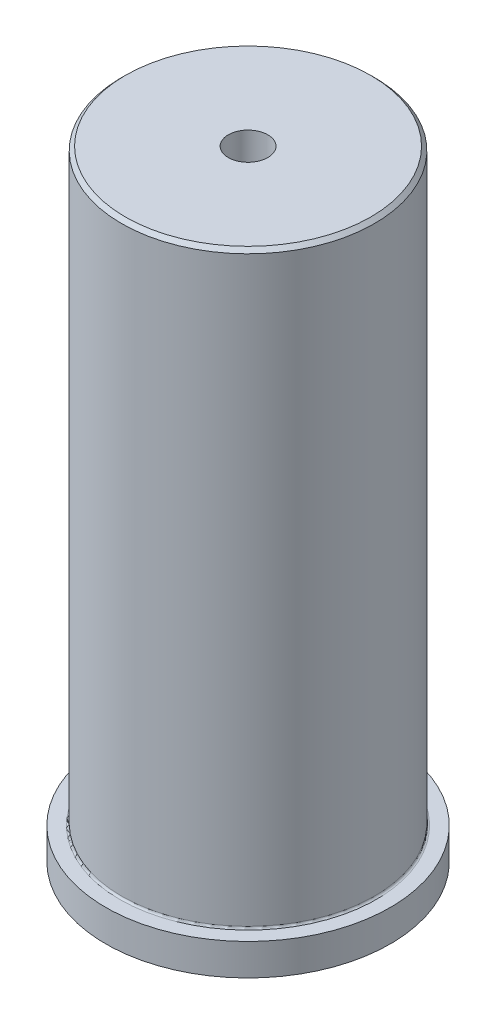
SolidWorks part; units mm, degrees
material "304 SSTL"
ref_plane "XY" through (0, 0, 0) normal (0, 0, 1) x (1, 0, 0)
ref_plane "XZ" through (0, 0, 0) normal (0, 1, 0) x (1, 0, 0)
ref_plane "YZ" through (0, 0, 0) normal (1, 0, 0) x (0, 0, -1)
sketch "Sketch1" plane through (0, 0, 0) normal (0, 0, 1) x (1, 0, 0)
  line L0 (0, 0) -> (0, 104.2377) construction
  line L1 (0, 0) -> (28.575, 0)
  line L2 (28.575, 0) -> (28.575, 6.35)
  line L3 (28.575, 6.35) -> (25.4, 6.35)
  line L4 (25.4, 6.35) -> (25.4, 124.46)
  line L5 (25.4, 124.46) -> (0, 124.46)
  line L6 (0, 124.46) -> (0, 0)
  dimension "D1" = 50.8
  dimension "D2" = 57.15
  dimension "D3" = 118.11
  dimension "D4" = 6.35
revolve "Revolve1" add sketch "Sketch1" angle 360 about L0
sketch "Sketch2" plane through (0, 124.46, 0) normal (0, 1, 0) x (-1, 0, 0)
  circle A0 centre (0, 0) radius 4.2164 construction
  circle A1 centre (0, 0) radius 25.4 construction
  dimension "D1" = 8.4328
hole_wizard "3/8-16 Tapped Hole1" positions "3DSketch1" profile "Sketch3" tap size "3/8-16" standard "Ansi Inch"
sketch3d "3DSketch1"
  point P0 (0, 124.46, 0)
sketch "Sketch3" plane through (0, 124.46, 0) normal (1, 0, 0) x (0, 0, 1)
  line L0 (0, 0) -> (0, 31.9249)
  line L1 (0, 31.9249) -> (3.9687, 29.5402)
  line L2 (3.9687, 29.5402) -> (3.9687, 0)
  line L5 (3.9687, 0) -> (0, 0)
  line L10 (0, 31.9249) -> (-3.9688, 29.5402) construction
  line L11 (0, -6.35) -> (0, 107.95) construction
  dimension "Tap Drill Dia." = 7.9375
  dimension "Tap Drill Depth" = 29.5402
  dimension "Drill Angle" = 118
cosmetic thread "Cosmetic Thread1" parameters "D1"=21.59, "D2"=9.525
chamfer "Chamfer1" distance 0.762 angle 45 1 edges at (0, 124.46, -25.4)
fillet "Fillet1" radius 0.381 1 edges at (0, 6.35, -25.4)
sketch "Sketch4" plane through (0, 0, 0) normal (0, 0, 1) x (1, 0, 0)
  line L0 (-3.9687, 94.9198) -> (0, 92.5351)
  line L1 (-3.9687, 94.9198) -> (0, 92.5351) construction
  line L2 (0, 92.5351) -> (3.9687, 94.9198)
  line L3 (0, 92.5351) -> (3.9687, 94.9198) construction
  line L4 (-3.9687, 124.46) -> (-3.9687, 94.9198)
  line L5 (-3.9687, 124.46) -> (-3.9687, 94.9198) construction
  line L6 (3.9687, 94.9198) -> (3.9687, 124.46)
  line L7 (3.9687, 94.9198) -> (3.9687, 124.46) construction
  line L8 (-3.9687, 94.9198) -> (3.9687, 94.9198) construction
  circle A0 centre (0, 94.9198) radius 1.5875
  dimension "D1" = 3.175
extrude "Cut-Extrude1" cut sketch "Sketch4" against normal blind 27.94
